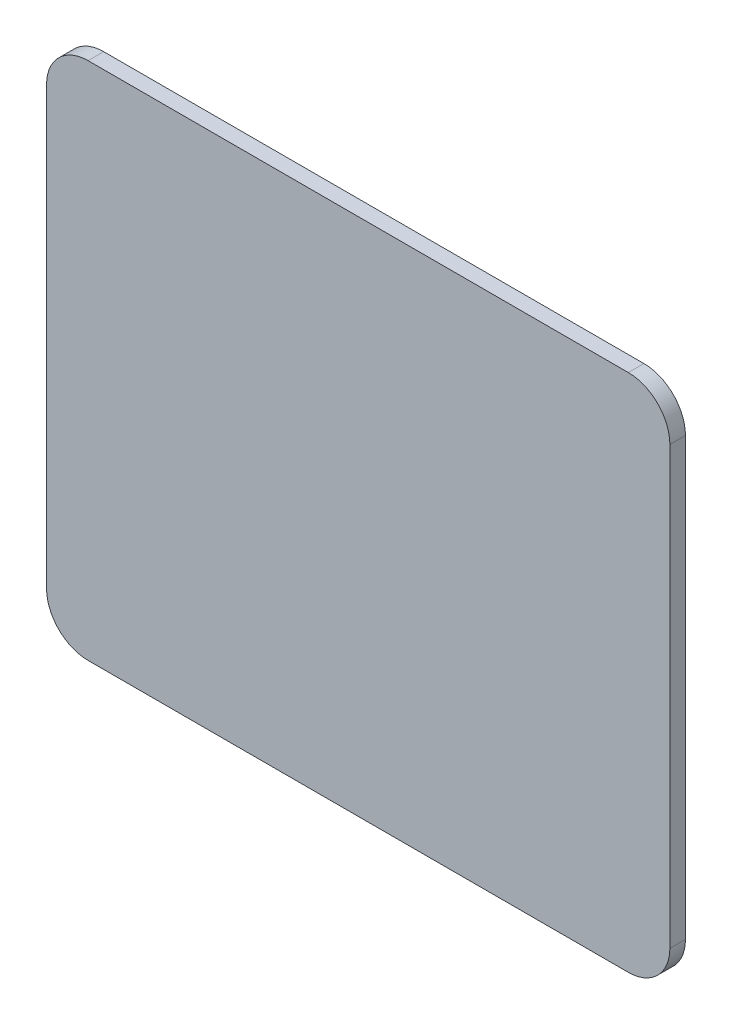
SolidWorks part; units mm, degrees
ref_plane "Front Plane" through (0, 0, 0) normal (0, 0, 1) x (1, 0, 0)
ref_plane "Top Plane" through (0, 0, 0) normal (0, 1, 0) x (1, 0, 0)
ref_plane "Right Plane" through (0, 0, 0) normal (1, 0, 0) x (0, 0, -1)
sketch "Sketch1" plane through (0, 0, 0) normal (0, 0, 1) x (1, 0, 0)
  line L0 (-72.1221, 155) -> (-72.1221, 71) construction
  line L1 (-64.1221, 63) -> (39.8779, 63) construction
  line L2 (39.8779, 163) -> (-64.1221, 163) construction
  line L3 (47.8779, 71) -> (47.8779, 155) construction
  line L4 (-72.1221, 155) -> (-72.1221, 71)
  line L5 (-64.1221, 63) -> (39.8779, 63)
  line L6 (39.8779, 163) -> (-64.1221, 163)
  line L7 (47.8779, 71) -> (47.8779, 155)
  arc A0 (-64.1221, 163) -> (-72.1221, 155) centre (-64.1221, 155) ccw construction
  arc A1 (-72.1221, 71) -> (-64.1221, 63) centre (-64.1221, 71) ccw construction
  arc A2 (39.8779, 63) -> (47.8779, 71) centre (39.8779, 71) ccw construction
  arc A3 (47.8779, 155) -> (39.8779, 163) centre (39.8779, 155) ccw construction
  arc A4 (-64.1221, 163) -> (-72.1221, 155) centre (-64.1221, 155) ccw
  arc A5 (-72.1221, 71) -> (-64.1221, 63) centre (-64.1221, 71) ccw
  arc A6 (39.8779, 63) -> (47.8779, 71) centre (39.8779, 71) ccw
  arc A7 (47.8779, 155) -> (39.8779, 163) centre (39.8779, 155) ccw
extrude "Boss-Extrude1" add sketch "Sketch1" against normal blind 3
